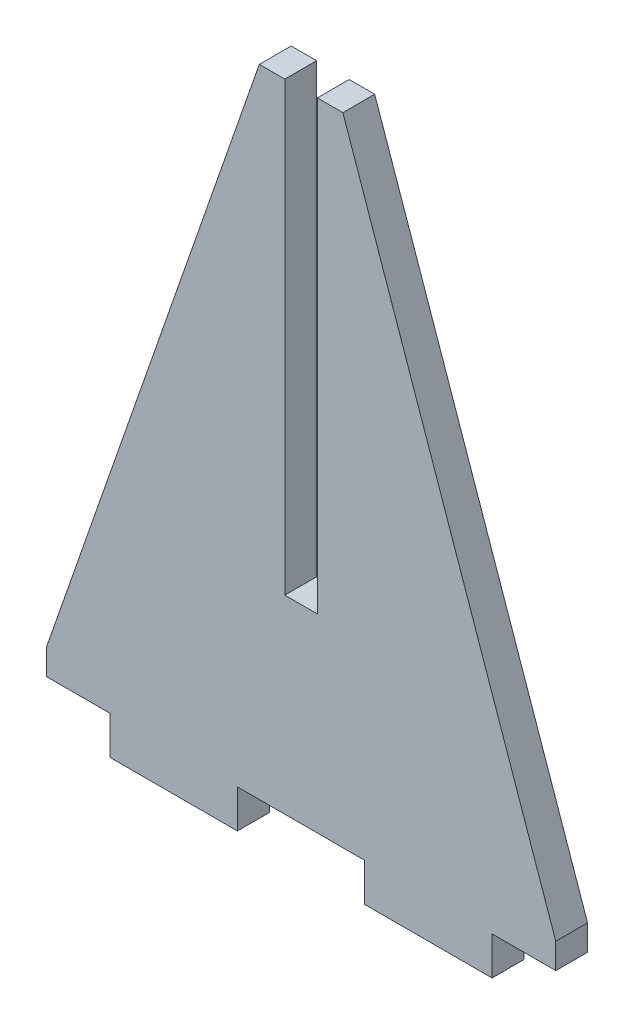
SolidWorks part; units mm, degrees
ref_plane "Front Plane" through (0, 0, 0) normal (0, 0, 1) x (1, 0, 0)
ref_plane "Top Plane" through (0, 0, 0) normal (0, 1, 0) x (1, 0, 0)
ref_plane "Right Plane" through (0, 0, 0) normal (1, 0, 0) x (0, 0, -1)
sketch "Sketch1" plane through (0, 0, 0) normal (0, 0, 1) x (1, 0, 0)
  line L0 (-1.6256, 18.923) -> (-1.6256, 63.5)
  line L7 (1.6256, 18.923) -> (-1.6256, 18.923)
  line L10 (1.6256, 18.923) -> (1.6256, 63.5)
  line L11 (0, 0) -> (0, 18.923) construction
  line L12 (-19.05, 0) -> (-19.05, -3.81)
  line L15 (-6.35, -3.81) -> (-6.35, 0)
  line L16 (-19.05, 0) -> (-25.4, 0)
  line L26 (-19.05, -3.81) -> (-6.35, -3.81)
  line L27 (-6.35, 0) -> (0, 0)
  line L28 (0, 0) -> (6.35, 0)
  line L29 (6.35, 0) -> (6.35, -3.81)
  line L30 (6.35, -3.81) -> (19.05, -3.81)
  line L31 (19.05, -3.81) -> (19.05, 0)
  line L32 (19.05, 0) -> (25.4, 0)
  line L33 (1.6256, 63.5) -> (4.1656, 63.5)
  line L34 (-1.6256, 63.5) -> (-4.1656, 63.5)
  line L36 (25.4, 0) -> (25.4, 2.54)
  line L37 (25.4, 2.54) -> (4.1656, 63.5)
  line L38 (-25.4, 0) -> (-25.4, 2.54)
  line L39 (-25.4, 2.54) -> (-4.1656, 63.5)
  point P2 (0, 0)
  point P9 (0, 0)
  dimension "D1" = 6.35
  dimension "D2" = 12.7
  dimension "D3" = 6.35
  dimension "D4" = 12.7
  dimension "D5" = 6.35
  dimension "D6" = 3.81
  dimension "D7" = 6.35
  dimension "D8" = 2.54
  dimension "D9" = 2.54
  dimension "D10" = 2.54
  dimension "D11" = 2.54
  dimension "D12" = 3.2512
  dimension "D13" = 18.923
  dimension "D14" = 63.5
extrude "Boss-Extrude1" add sketch "Sketch1" along normal blind 3.175
